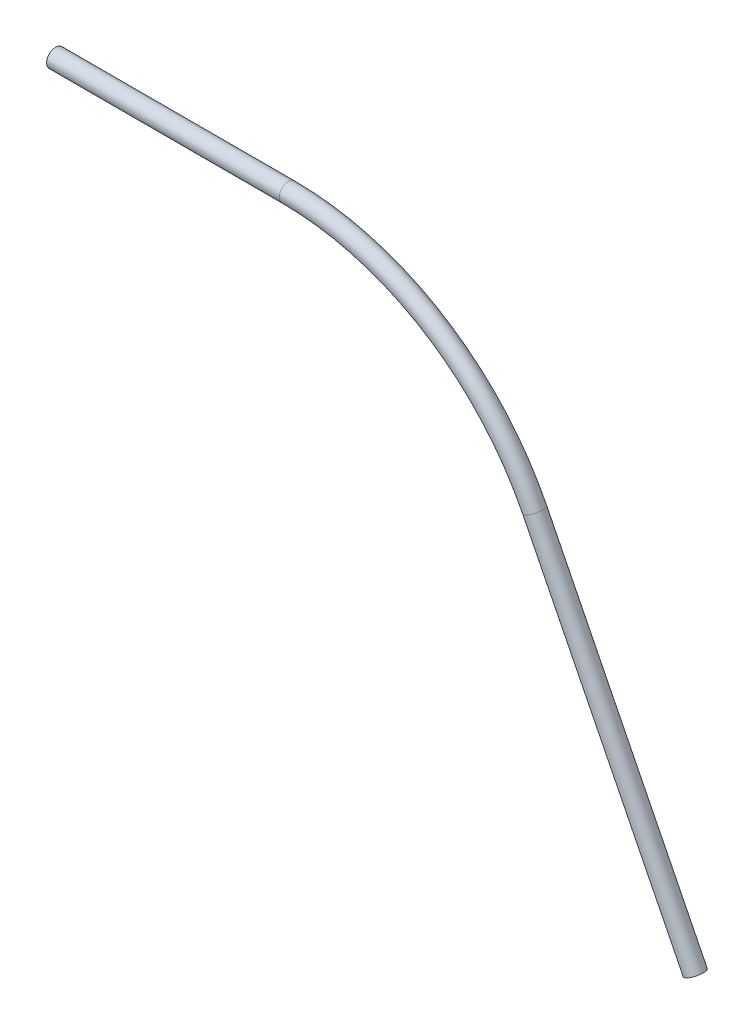
SolidWorks part; units mm, degrees
ref_plane "Front Plane" through (0, 0, 0) normal (0, 0, 1) x (1, 0, 0)
ref_plane "Top Plane" through (0, 0, 0) normal (0, 1, 0) x (1, 0, 0)
ref_plane "Right Plane" through (0, 0, 0) normal (1, 0, 0) x (0, 0, -1)
sketch "Sketch1" plane through (0, 0, 0) normal (1, 0, 0) x (0, 0, -1)
  circle A0 centre (0, 0) radius 0.62
  circle A1 centre (0, 0) radius 0.498
  dimension "D1" = 1.24
  dimension "D2" = 0.996
sketch "Sketch2" plane through (0, 0, 0) normal (0, 0, 1) x (1, 0, 0)
  line L0 (0, 0) -> (16.0455, 0)
  line L1 (33.0333, -10.4902) -> (44.1027, -32.5877)
  arc A0 (16.0455, 0) -> (33.0333, -10.4902) centre (16.0455, -19) cw
  dimension "D1" = 19
sweep "Sweep1" add profiles "Sketch1" path "Sketch2"
